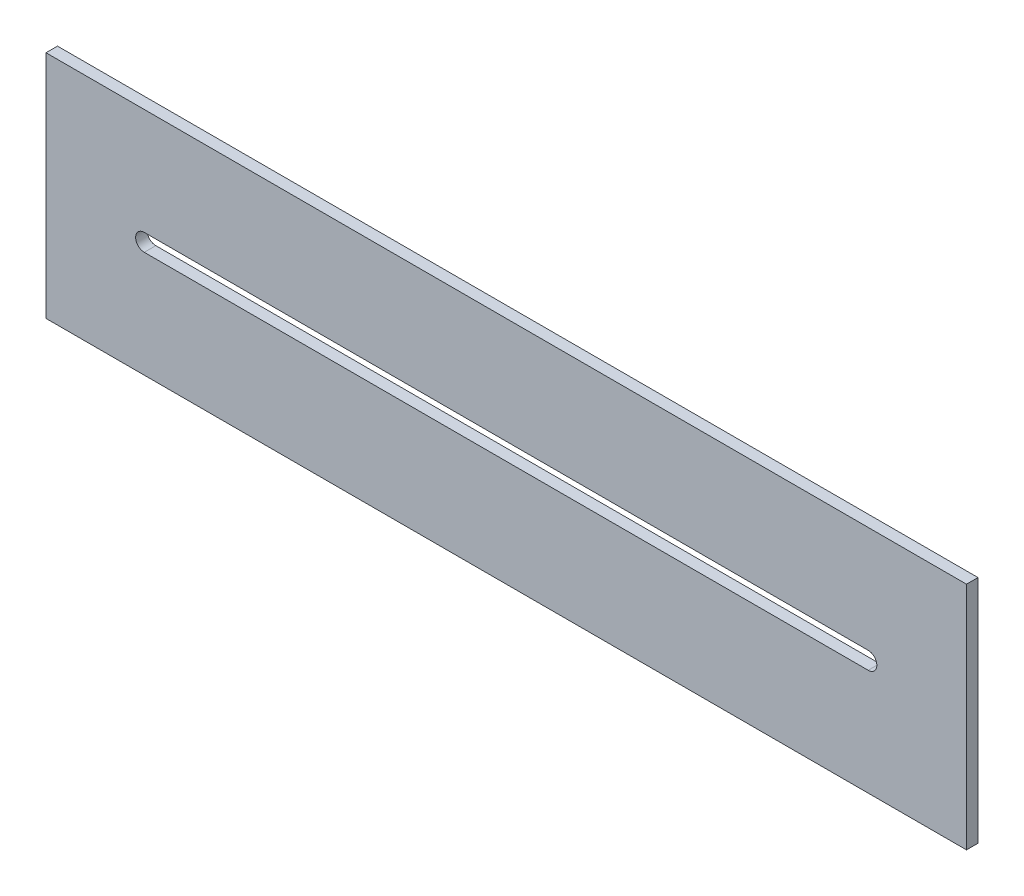
SolidWorks part; units mm, degrees
ref_plane "Front Plane" through (0, 0, 0) normal (0, 0, 1) x (1, 0, 0)
ref_plane "Top Plane" through (0, 0, 0) normal (0, 1, 0) x (1, 0, 0)
ref_plane "Right Plane" through (0, 0, 0) normal (1, 0, 0) x (0, 0, -1)
sketch "Sketch1" plane through (0, 0, 111.506) normal (0, 0, 1) x (1, 0, 0)
  line L0 (-52.165, 3.4913) -> (107.6503, 3.4913) construction
  line L1 (-73.8574, 28.8913) -> (129.3426, 28.8913)
  line L2 (-73.8574, 28.8913) -> (-73.8574, -21.9087)
  line L3 (-73.8574, -21.9087) -> (129.3426, -21.9087)
  line L4 (129.3426, 28.8913) -> (129.3426, -21.9087)
  line L5 (-52.165, 5.3963) -> (107.6503, 5.3963)
  line L6 (-52.165, 1.5863) -> (107.6503, 1.5863)
  arc A0 (-52.165, 5.3963) -> (-52.165, 1.5863) centre (-52.165, 3.4913) ccw
  arc A1 (107.6503, 1.5863) -> (107.6503, 5.3963) centre (107.6503, 3.4913) ccw
  point P6 (27.7426, 3.4913)
  point P11 (129.3426, 3.4913)
  dimension "D1" = 203.2
  dimension "D2" = 50.8
  dimension "D3" = 3.81
extrude "Boss-Extrude1" add sketch "Sketch1" against normal blind 2.54
